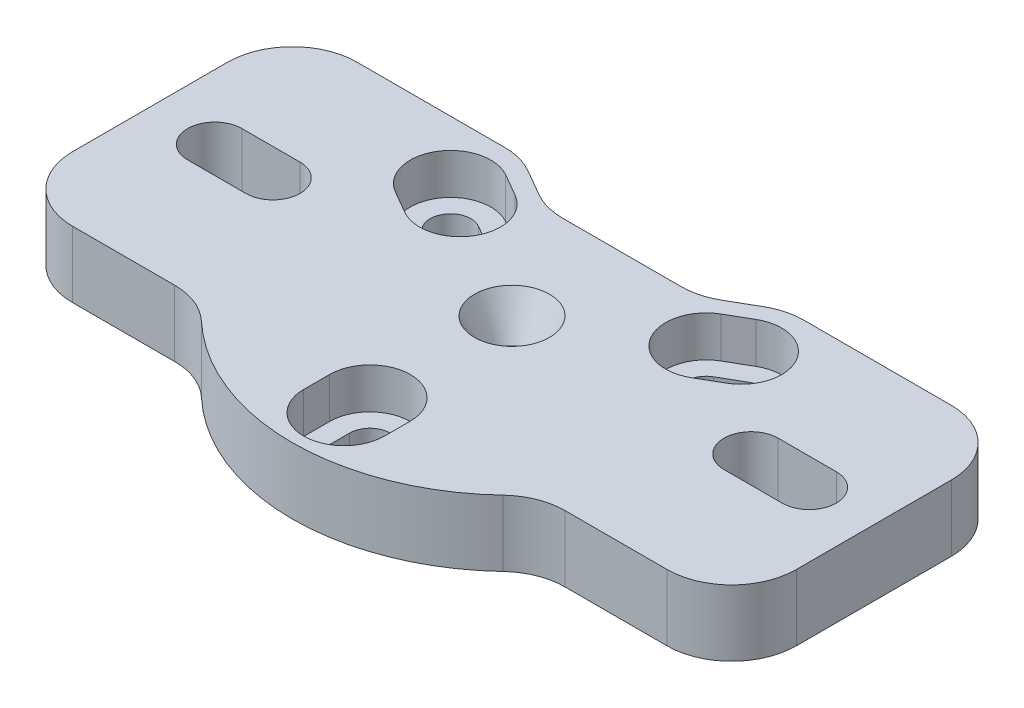
SolidWorks part; units mm, degrees
material "CA"
ref_plane "Front Plane" through (0, 0, 0) normal (0, 0, 1) x (1, 0, 0)
ref_plane "Top Plane" through (0, 0, 0) normal (0, 1, 0) x (1, 0, 0)
ref_plane "Right Plane" through (0, 0, 0) normal (1, 0, 0) x (0, 0, -1)
sketch "Sketch1" plane through (0, 0, 0) normal (0, 1, 0) x (1, 0, 0)
  line L0 (14.7222, 13.97) -> (29.21, 13.97)
  line L1 (-29.21, 13.97) -> (-14.7222, 13.97)
  line L2 (-35.56, 7.62) -> (-35.56, -7.62)
  line L3 (-11.5472, 13.1193) -> (-8.995, 11.6457)
  line L4 (35.56, 7.62) -> (35.56, -7.62)
  line L5 (-23.495, 0) -> (-29.21, 0) construction
  line L6 (-23.495, -2.667) -> (-29.21, -2.667)
  line L7 (-23.495, 2.667) -> (-29.21, 2.667)
  line L8 (23.495, 0) -> (29.21, 0) construction
  line L9 (23.495, 2.667) -> (29.21, 2.667)
  line L10 (23.495, -2.667) -> (29.21, -2.667)
  line L11 (-14.2894, 8.25) -> (0, 0) construction
  line L12 (0, 0) -> (14.2894, 8.25) construction
  line L13 (-15.2894, 6.5179) -> (-13.0897, 5.2479)
  line L14 (-13.2894, 9.9821) -> (-11.0897, 8.7121)
  line L15 (13.2894, 9.9821) -> (11.0897, 8.7121)
  line L16 (15.2894, 6.5179) -> (13.0897, 5.2479)
  line L17 (2, -16.5) -> (2, -13.96)
  line L18 (-2, -13.96) -> (-2, -16.5)
  line L19 (-29.21, -13.97) -> (-19.1766, -13.97)
  line L20 (19.1766, -13.97) -> (29.21, -13.97)
  line L21 (-5.82, 10.795) -> (5.82, 10.795)
  line L22 (8.995, 11.6457) -> (11.5472, 13.1193)
  circle A0 centre (0, 0) radius 1.778
  arc A1 (-23.495, -2.667) -> (-23.495, 2.667) centre (-23.495, 0) ccw
  arc A2 (-29.21, 2.667) -> (-29.21, -2.667) centre (-29.21, 0) ccw
  arc A3 (23.495, 2.667) -> (23.495, -2.667) centre (23.495, 0) ccw
  arc A4 (29.21, -2.667) -> (29.21, 2.667) centre (29.21, 0) ccw
  arc A5 (-13.2894, 9.9821) -> (-15.2894, 6.5179) centre (-14.2894, 8.25) ccw
  arc A6 (15.2894, 6.5179) -> (13.2894, 9.9821) centre (14.2894, 8.25) ccw
  circle A7 centre (0, 0) radius 20 construction
  arc A8 (29.21, 13.97) -> (35.56, 7.62) centre (29.21, 7.62) cw
  arc A9 (29.21, -13.97) -> (35.56, -7.62) centre (29.21, -7.62) ccw
  arc A10 (19.1766, -13.97) -> (14.8183, -15.7018) centre (19.1766, -20.32) ccw
  arc A11 (-29.21, 13.97) -> (-35.56, 7.62) centre (-29.21, 7.62) ccw
  circle A12 centre (0, 0) radius 16.5 construction
  arc A13 (-2, -16.5) -> (2, -16.5) centre (0, -16.5) ccw
  arc A14 (5.82, 10.795) -> (8.995, 11.6457) centre (5.82, 17.145) ccw
  arc A15 (11.5472, 13.1193) -> (14.7222, 13.97) centre (14.7222, 7.62) cw
  arc A16 (-14.7222, 13.97) -> (-11.5472, 13.1193) centre (-14.7222, 7.62) cw
  arc A17 (-13.0897, 5.2479) -> (-11.0897, 8.7121) centre (-12.0897, 6.98) ccw
  arc A18 (11.0897, 8.7121) -> (13.0897, 5.2479) centre (12.0897, 6.98) ccw
  arc A19 (2, -13.96) -> (-2, -13.96) centre (0, -13.96) ccw
  arc A20 (-14.8183, -15.7018) -> (14.8183, -15.7018) centre (0, 0) ccw
  arc A21 (-19.1766, -13.97) -> (-14.8183, -15.7018) centre (-19.1766, -20.32) cw
  arc A22 (-29.21, -13.97) -> (-35.56, -7.62) centre (-29.21, -7.62) cw
  arc A23 (-8.995, 11.6457) -> (-5.82, 10.795) centre (-5.82, 17.145) ccw
  point P9 (-26.3525, 0)
  point P14 (26.3525, 0)
  point P42 (11.6397, 13.97)
  point P50 (-16.4611, -13.97)
  dimension "D3" = 3.556
  dimension "D10" = 40
  dimension "D11" = 6.35
  dimension "D8" = 33
  dimension "D9" = 4
  dimension "D13" = 10.795
  dimension "D18" = 6.35
  dimension "D16" = 21.59
  dimension "D21" = 6.35
  dimension "D14" = 6.35
  dimension "D2" = 71.12
  dimension "D4" = 23.495
  dimension "D5" = 23.495
  dimension "D6" = 29.21
  dimension "D7" = 5.334
  dimension "D12" = 120
  dimension "D15" = 13.97
  dimension "D17" = 35.56
  dimension "D19" = 2.54
  dimension "D20" = 13.97
  dimension "D22" = 5.588
  dimension "D23" = 5.588
extrude "Boss-Extrude1" add sketch "Sketch1" along normal blind 6.5
sketch "Sketch5" plane through (0, 6.5, 0) normal (0, 1, 0) x (1, 0, 0)
  line L0 (-3.9688, -13.96) -> (-3.9688, -16.5)
  line L1 (3.9688, -16.5) -> (3.9688, -13.96)
  line L2 (12.305, 11.687) -> (10.1053, 10.417)
  line L3 (16.2738, 4.813) -> (14.0741, 3.543)
  line L4 (-12.305, 11.687) -> (-10.1053, 10.417)
  line L5 (-16.2738, 4.813) -> (-14.0741, 3.543)
  arc A0 (16.2738, 4.813) -> (12.305, 11.687) centre (14.2894, 8.25) ccw
  arc A1 (-12.305, 11.687) -> (-16.2738, 4.813) centre (-14.2894, 8.25) ccw
  arc A2 (-3.9688, -16.5) -> (3.9688, -16.5) centre (0, -16.5) ccw
  arc A3 (-14.0741, 3.543) -> (-10.1053, 10.417) centre (-12.0897, 6.98) ccw
  arc A4 (3.9688, -13.96) -> (-3.9688, -13.96) centre (0, -13.96) ccw
  arc A5 (10.1053, 10.417) -> (14.0741, 3.543) centre (12.0897, 6.98) ccw
  dimension "D1" = 7.9375
extrude "Cut-Extrude1" cut sketch "Sketch5" against normal blind 4
ref_plane "Plane1" through (0, 0, 0) normal (0.5, 0, 0.866) x (0.866, 0, -0.5)
chamfer "Chamfer1" distance 1.905 distance2 3.81 1 edges at (0, 6.5, 1.778)
